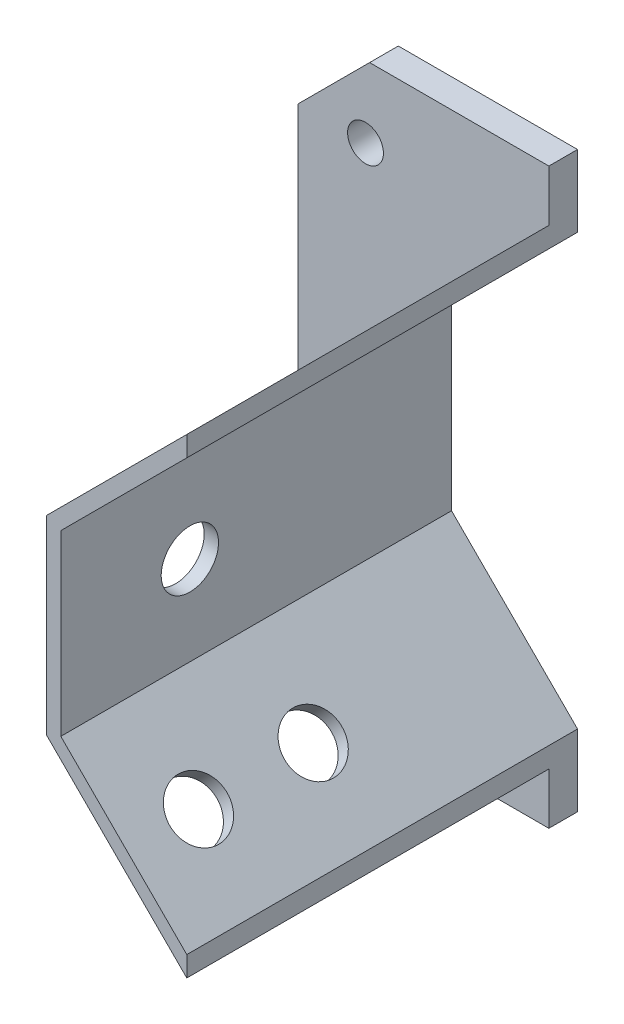
SolidWorks part; units mm, degrees
ref_plane "前视基准面" through (0, 0, 0) normal (0, 0, 1) x (1, 0, 0)
ref_plane "上视基准面" through (0, 0, 0) normal (0, 1, 0) x (1, 0, 0)
ref_plane "右视基准面" through (0, 0, 0) normal (1, 0, 0) x (0, 0, -1)
sketch "草图1" plane through (0, 0, 0) normal (0, 0, 1) x (1, 0, 0)
  line L0 (-21.2132, -21.2132) -> (-32.5858, -32.5858) construction
  line L1 (-21.2132, 21.2132) -> (-34.0926, 34.0926) construction
  line L2 (0, 0) -> (20.0292, 0) construction
  line L3 (-12.4264, 30) -> (-30, 12.4264)
  line L4 (-12.4264, -30) -> (-30, -12.4264)
  line L5 (-30, 12.4264) -> (-30, -12.4264)
  line L6 (-12.4264, 32.8284) -> (-32, 13.2548)
  line L7 (-32, 13.2548) -> (-32, -13.2548)
  line L8 (-12.4264, -32.8284) -> (-32, -13.2548)
  line L9 (-12.4264, -30) -> (-12.4264, -32.8284)
  line L11 (-12.4264, 30) -> (-12.4264, 32.8284)
  line L12 (-13.8406, 31.4142) -> (-32, 13.2548) construction
  line L13 (-13.8406, -31.4142) -> (-32, -13.2548) construction
  circle A0 centre (0, 0) radius 30 construction
  dimension "D1" = 60
  dimension "D2" = 45
  dimension "D3" = 45
  dimension "D4" = 2
extrude "凸台-拉伸1" add sketch "草图1" along normal blind 50.5
sketch "草图2" plane through (0, 0, 0) normal (0, 0, -1) x (-1, 0, 0)
  line L0 (12.4264, 30) -> (12.4264, 40)
  line L1 (12.4264, 40) -> (47.4264, 40)
  line L2 (47.4264, 40) -> (47.4264, -40)
  line L3 (47.4264, -40) -> (12.4264, -40)
  line L4 (12.4264, -40) -> (12.4264, -30)
  line L5 (30, 12.4264) -> (12.4264, 30) construction
  line L6 (30, 12.4264) -> (12.4264, 30)
  line L7 (30, -12.4264) -> (30, 12.4264) construction
  line L8 (12.4264, -30) -> (30, -12.4264) construction
  line L9 (30, -12.4264) -> (30, 12.4264)
  line L10 (12.4264, -30) -> (30, -12.4264)
  dimension "D1" = 10
  dimension "D2" = 10
  dimension "D3" = 35
extrude "凸台-拉伸2" add sketch "草图2" along normal blind 4
chamfer "倒角1" distance 10 angle 45 2 edges at (-47.4264, -40, -2) (-47.4264, 40, -2)
sketch "草图3" plane through (-22.6274, 22.6274, 0) normal (-0.7071, 0.7071, 0) x (0, 0, 1)
  line L0 (50.5, 14.4264) -> (50.5, -13.2548) construction
  circle A0 centre (40.5, 0.5858) radius 4
  circle A1 centre (24.5, 0.5858) radius 4
  dimension "D1" = 8
  dimension "D2" = 8
  dimension "D3" = 16
  dimension "D4" = 10
extrude "切除-拉伸1" cut sketch "草图3" against normal blind 10
sketch "草图4" plane through (-32, 0, 0) normal (-1, 0, 0) x (0, 0, 1)
  line L0 (50.5, 13.2548) -> (50.5, -13.2548) construction
  circle A0 centre (32.5, 0) radius 4
  dimension "D1" = 8
  dimension "D2" = 18
extrude "切除-拉伸2" cut sketch "草图4" against normal blind 10
mirror "镜向1" about plane through (0, 0, 0) normal (0, 1, 0) of "切除-拉伸1"
sketch "草图5" plane through (0, 0, 0) normal (0, 0, 1) x (1, 0, 0)
  line L0 (0, 0) -> (-64.3571, 0) construction
  circle A0 centre (-38, 30) radius 2.5
  circle A1 centre (-38, -30) radius 2.5
  dimension "D2" = 30
  dimension "D3" = 5
  dimension "D1" = 38
extrude "切除-拉伸3" cut sketch "草图5" against normal blind 10
